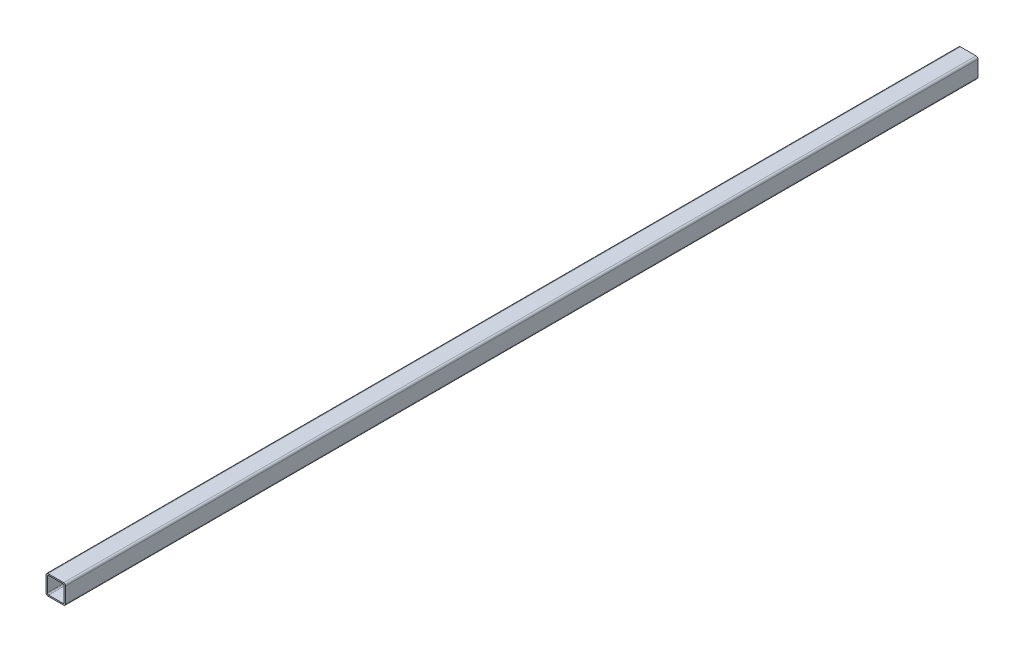
SolidWorks part; units mm, degrees
material "AISI 1020"
ref_plane "Спереди" through (0, 0, 0) normal (0, 0, 1) x (1, 0, 0)
ref_plane "Сверху" through (0, 0, 0) normal (0, 1, 0) x (1, 0, 0)
ref_plane "Справа" through (0, 0, 0) normal (1, 0, 0) x (0, 0, -1)
sketch "Эскиз1" plane through (0, 0, 0) normal (0, 0, 1) x (1, 0, 0)
  line L0 (1.6111, 40.6112) -> (1.6111, -40.6112) construction
  point P2 (-0.3889, 0)
  line B0 (-25.3889, 15) -> (-1.3889, 15)
  line B1 (-28.3889, 12) -> (-28.3889, -12)
  line B2 (-25.3889, -15) -> (-1.3889, -15)
  line B3 (1.6111, 12) -> (1.6111, -12)
  line B4 (-24.3889, 13) -> (-2.3889, 13)
  line B5 (-26.3889, 11) -> (-26.3889, -11)
  line B6 (-24.3889, -13) -> (-2.3889, -13)
  line B7 (-0.3889, 11) -> (-0.3889, -11)
  arc B8 (-28.3889, -12) -> (-25.3889, -15) centre (-25.3889, -12) ccw
  arc B9 (-1.3889, -15) -> (1.6111, -12) centre (-1.3889, -12) ccw
  arc B10 (-1.3889, 15) -> (1.6111, 12) centre (-1.3889, 12) cw
  arc B11 (-25.3889, 15) -> (-28.3889, 12) centre (-25.3889, 12) ccw
  arc B12 (-26.3889, -11) -> (-24.3889, -13) centre (-24.3889, -11) ccw
  arc B13 (-2.3889, -13) -> (-0.3889, -11) centre (-2.3889, -11) ccw
  arc B14 (-2.3889, 13) -> (-0.3889, 11) centre (-2.3889, 11) cw
  arc B15 (-24.3889, 13) -> (-26.3889, 11) centre (-24.3889, 11) ccw
sketch_block_instance "Блок-30х30х2-1"
sketch_block "Блок-30х30х2" parameters "D3"=3, "D4"=2, "D1"=30, "D2"=2
extrude "Бобышка-Вытянуть1" add sketch "Эскиз1" along normal up to surface (700 mm away)
mirror "Зеркальное отражение1" about plane through (-25.3889, -12, 0) normal (0, 0, 1) of bodies 103
